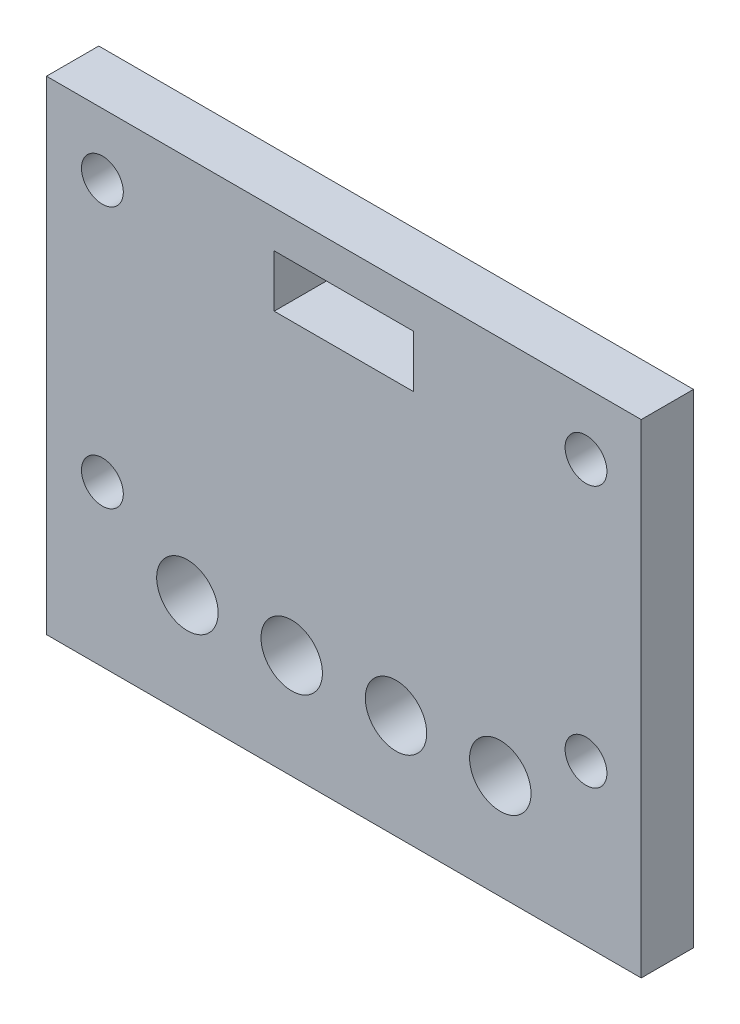
SolidWorks part; units mm, degrees
ref_plane "Front Plane" through (0, 0, 0) normal (0, 0, 1) x (1, 0, 0)
ref_plane "Top Plane" through (0, 0, 0) normal (0, 1, 0) x (1, 0, 0)
ref_plane "Right Plane" through (0, 0, 0) normal (1, 0, 0) x (0, 0, -1)
sketch "Sketch1" plane through (0, 0, 0) normal (0, 0, 1) x (1, 0, 0)
  line L1 (0, 0) -> (45.5, 0)
  line L2 (0, 0) -> (0, 37)
  line L3 (0, 37) -> (45.5, 37)
  line L4 (45.5, 0) -> (45.5, 37)
  line L7 (17.42, 34.14) -> (28.08, 34.14)
  line L8 (17.42, 34.14) -> (17.42, 30.14)
  line L9 (17.42, 30.14) -> (28.08, 30.14)
  line L10 (28.08, 34.14) -> (28.08, 30.14)
  line L11 (17.42, 34.14) -> (28.08, 30.14) construction
  line L12 (17.42, 30.14) -> (28.08, 34.14) construction
  line L13 (17.42, 30.14) -> (28.08, 30.14) construction
  point P4 (22.75, 18.5)
  point P11 (22.75, 32.14)
  dimension "D1" = 4
  dimension "D2" = 10.66
  dimension "D3" = 17.42
  dimension "D4" = 30.14
extrude "Boss-Extrude1" add sketch "Sketch1" along normal blind 4
sketch "Sketch3" plane through (0, 0, 0) normal (0, 0, 1) x (1, 0, 0)
  line L5 (0.0517, 0) -> (45.5, 0) construction
  line L6 (4.2758, 32.2526) -> (41.2758, 32.2526) construction
  line L7 (4.2758, 32.2526) -> (4.2758, 12.2526) construction
  line L8 (4.2758, 12.2526) -> (41.2758, 12.2526) construction
  line L9 (41.2758, 12.2526) -> (41.2758, 32.2526) construction
  circle A0 centre (41.2758, 32.2526) radius 1.6
  circle A1 centre (4.2758, 32.2526) radius 1.6
  circle A2 centre (4.2758, 12.2526) radius 1.6
  circle A3 centre (41.2758, 12.2526) radius 1.6
  point P8 (22.7758, 12.2526)
  point P13 (22.7758, 0)
  dimension "D1" = 4.2242
  dimension "D5" = 3.2
  dimension "D2" = 37
  dimension "D3" = 20
  dimension "D4" = 12.2526
extrude "Cut-Extrude5" cut sketch "Sketch3" along normal blind 10 and the other way through all contours A0 | A3 | A2 | A1
sketch "Sketch4" plane through (0, 0, 4) normal (0, 0, 1) x (1, 0, 0)
  line L0 (45.5, 0) -> (45.5, 8) construction
  line L1 (45.5, 0) -> (45.5, 37) construction
  line L2 (45.5, 8) -> (34.72, 8) construction
  line L3 (26.74, 8) -> (18.76, 8) construction
  line L4 (18.76, 8) -> (10.78, 8) construction
  line L5 (10.78, 8) -> (0, 8) construction
  line L6 (0, 37) -> (0, 0) construction
  line L7 (26.74, 8) -> (34.72, 8) construction
  circle A0 centre (10.78, 8) radius 2.35
  circle A1 centre (18.76, 8) radius 2.35
  circle A2 centre (26.74, 8) radius 2.35
  circle A3 centre (34.72, 8) radius 2.35
  dimension "D1" = 4.7
  dimension "D2" = 7.98
  dimension "D3" = 8
extrude "Lego gaten" cut sketch "Sketch4" against normal blind 10
